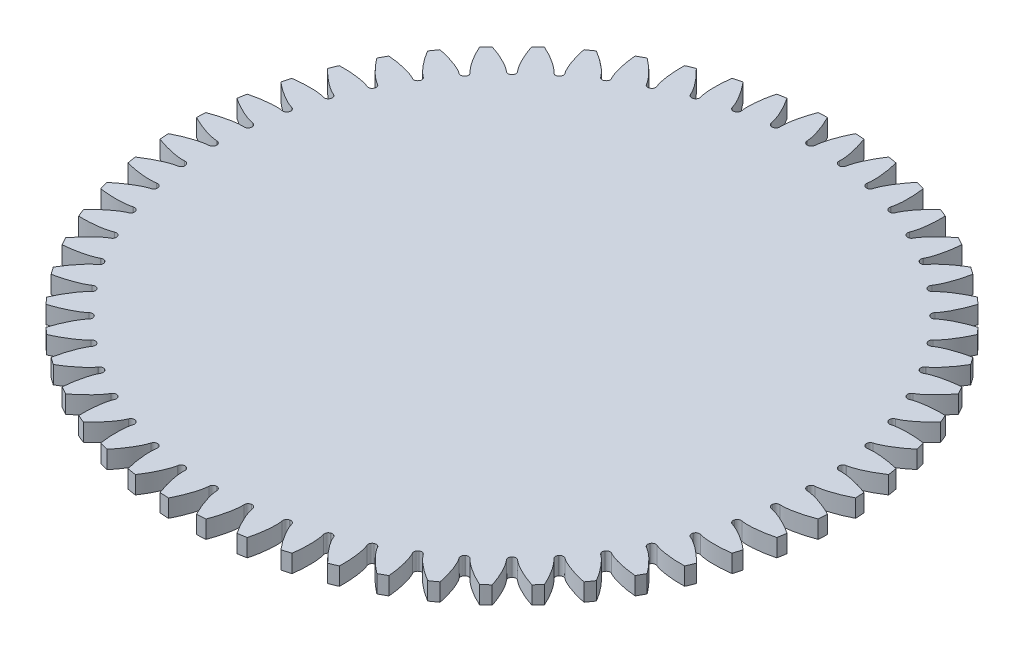
SolidWorks part; units mm, degrees
ref_plane "Front Plane" through (0, 0, 0) normal (0, 0, 1) x (1, 0, 0)
ref_plane "Top Plane" through (0, 0, 0) normal (0, 1, 0) x (1, 0, 0)
ref_plane "Right Plane" through (0, 0, 0) normal (1, 0, 0) x (0, 0, -1)
sketch "Sketch1" plane through (0, 0, 0) normal (0, 1, 0) x (1, 0, 0)
  circle A0 centre (0, 0) radius 118.3821
  dimension "D1" = 236.7643
extrude "Boss-Extrude1" add sketch "Sketch1" along normal blind 6.35
sketch "Sketch2" plane through (0, 6.35, 0) normal (0, 1, 0) x (1, 0, 0)
  line L0 (107.3976, 1.4119) -> (106.0132, 1.3937)
  line L1 (107.3976, -1.4119) -> (106.0132, -1.3937)
  line L2 (0, 0) -> (107.3976, 1.4119) construction
  line L3 (0, 0) -> (107.3976, -1.4119) construction
  arc A0 (118.2747, -5.0436) -> (118.2747, 5.0436) centre (0, 0) ccw
  circle A1 centre (0, 0) radius 114.3 construction
  circle A2 centre (0, 0) radius 107.4069 construction
  circle A3 centre (0, 0) radius 106.0223 construction
  arc A4 (106.0132, -1.3937) -> (106.0132, 1.3937) centre (0, 0) ccw
  spline S0 degree 4 poles (107.3976, 1.4119) (107.4146, 1.4123) (107.4625, 1.4139) (107.5528, 1.419) (107.7003, 1.4302) (107.8881, 1.4488) (108.1307, 1.4777) (108.4164, 1.5181) (108.7303, 1.5692) (109.0716, 1.6318) (109.4119, 1.7007) (109.7512, 1.7752) (110.089, 1.8548) (110.498, 1.9576) (110.9882, 2.0895) (111.5606, 2.2564) (112.2092, 2.4609) (112.8695, 2.6853) (113.5186, 2.9195) (114.1737, 3.1713) (114.8071, 3.4258) (115.4642, 3.7058) (116.0703, 3.9723) (116.7485, 4.2882) (117.2956, 4.5482) (118.0161, 4.9097) (118.4413, 5.1287) (118.9386, 5.3914) (119.1593, 5.5115) (119.2952, 5.5854) knots 0 0 0 0 0 0.005377 0.015084 0.028532 0.04661 0.064855 0.092111 0.119476 0.146842 0.174209 0.201575 0.228941 0.256307 0.307035 0.361767 0.4165 0.471232 0.525964 0.580697 0.635429 0.690161 0.744894 0.799626 0.854358 0.909091 0.954545 1 1 1 1 1 construction
  spline S1 degree 4 poles (107.3976, 1.4119) (107.4146, 1.4123) (107.4625, 1.4139) (107.5528, 1.419) (107.7003, 1.4302) (107.8881, 1.4488) (108.1307, 1.4777) (108.4164, 1.5181) (108.7303, 1.5692) (109.0716, 1.6318) (109.4119, 1.7007) (109.7512, 1.7752) (110.089, 1.8548) (110.498, 1.9576) (110.9882, 2.0895) (111.5606, 2.2564) (112.2092, 2.4609) (112.8695, 2.6853) (113.5186, 2.9195) (114.1737, 3.1713) (114.8071, 3.4258) (115.4642, 3.7058) (116.0703, 3.9723) (116.7485, 4.2882) (117.2956, 4.5482) (117.8599, 4.8313) (118.1344, 4.9712) (118.2747, 5.0436) knots 0 0 0 0 0 0.005377 0.015084 0.028532 0.04661 0.064855 0.092111 0.119476 0.146842 0.174209 0.201575 0.228941 0.256307 0.307035 0.361767 0.4165 0.471232 0.525964 0.580697 0.635429 0.690161 0.744894 0.799626 0.854358 0.909091 0.909091 0.909091 0.909091 0.909091
  spline S2 degree 4 poles (107.3976, -1.4119) (107.4146, -1.4123) (107.4625, -1.4139) (107.5528, -1.419) (107.7003, -1.4302) (107.8881, -1.4488) (108.1307, -1.4777) (108.4164, -1.5181) (108.7303, -1.5692) (109.0716, -1.6318) (109.4119, -1.7007) (109.7512, -1.7752) (110.089, -1.8548) (110.498, -1.9576) (110.9882, -2.0895) (111.5606, -2.2564) (112.2092, -2.4609) (112.8695, -2.6853) (113.5186, -2.9195) (114.1737, -3.1713) (114.8071, -3.4258) (115.4642, -3.7058) (116.0703, -3.9723) (116.7485, -4.2882) (117.2956, -4.5482) (118.0161, -4.9097) (118.4413, -5.1287) (118.9386, -5.3914) (119.1593, -5.5115) (119.2952, -5.5854) knots 0 0 0 0 0 0.005377 0.015084 0.028532 0.04661 0.064855 0.092111 0.119476 0.146842 0.174209 0.201575 0.228941 0.256307 0.307035 0.361767 0.4165 0.471232 0.525964 0.580697 0.635429 0.690161 0.744894 0.799626 0.854358 0.909091 0.954545 1 1 1 1 1 construction
  spline S3 degree 4 poles (107.3976, -1.4119) (107.4146, -1.4123) (107.4625, -1.4139) (107.5528, -1.419) (107.7003, -1.4302) (107.8881, -1.4488) (108.1307, -1.4777) (108.4164, -1.5181) (108.7303, -1.5692) (109.0716, -1.6318) (109.4119, -1.7007) (109.7512, -1.7752) (110.089, -1.8548) (110.498, -1.9576) (110.9882, -2.0895) (111.5606, -2.2564) (112.2092, -2.4609) (112.8695, -2.6853) (113.5186, -2.9195) (114.1737, -3.1713) (114.8071, -3.4258) (115.4642, -3.7058) (116.0703, -3.9723) (116.7485, -4.2882) (117.2956, -4.5482) (117.8599, -4.8313) (118.1344, -4.9712) (118.2747, -5.0436) knots 0 0 0 0 0 0.005377 0.015084 0.028532 0.04661 0.064855 0.092111 0.119476 0.146842 0.174209 0.201575 0.228941 0.256307 0.307035 0.361767 0.4165 0.471232 0.525964 0.580697 0.635429 0.690161 0.744894 0.799626 0.854358 0.909091 0.909091 0.909091 0.909091 0.909091
  dimension "D2" = 228.6
  dimension "D3" = 214.8137
  dimension "D4" = 212.0446
extrude "Cut-Extrude1" cut sketch "Sketch2" against normal up to next (6.35 mm away)
fillet "Fillet1" radius 1.3696 2 edges at (106.0132, 3.175, 1.3937) (106.0132, 3.175, -1.3937)
ref_axis "Axis1" through (0, 6.35, 0) along (0, -1, 0)
pattern_circular "CirPattern2" count 56 over 360 about axis through (0, 6.35, 0) along (0, -1, 0) of "Cut-Extrude1", "Fillet1"
equation "\"DiametralPitch\" = \"NumTeeth\" / 9"
equation "\"NumTeeth\" = 56"
equation "\"PressureAngle\" = 20"
equation "\"Addendum\"= 1 / \"DiametralPitch\""
equation "\"Dedendum\"= 1.25 / \"DiametralPitch\""
equation "\"WorkingDepth\"= 2 / \"DiametralPitch\""
equation "\"WholeDepth\"= 2.25 / \"DiametralPitch\""
equation "\"Clearance\"= 0.25 / \"DiametralPitch\""
equation "\"ToothThickness\"= 1.5708 / \"DiametralPitch\""
equation "\"CircularPitch\"= pi / \"DiametralPitch\""
equation "\"PitchCircle\"= \"NumTeeth\" / \"DiametralPitch\""
equation "\"OutsideDiameter\"= ( \"NumTeeth\" + 2 ) / \"DiametralPitch\""
equation "\"Fillet\"= \"Clearance\" * cos ( \"PressureAngle\" ) * tan ( ( 90 + \"PressureAngle\" ) / 2 )"
equation "\"AddendumCircle\"= \"PitchCircle\" + ( 2 * \"Addendum\" )"
equation "\"DedendumCircle\" = \"PitchCircle\" - ( 2 * \"Dedendum\" ) - .25"
equation "\"BaseCircle\"= \"PitchCircle\" * cos ( \"PressureAngle\" )"
equation "\"PitchAngle\"= 360deg / \"NumTeeth\""
equation "\"Alpha\"= sqr ( \"PitchCircle\" ^ 2 - \"BaseCircle\" ^ 2 ) / \"BaseCircle\" * 180 / PI - \"PressureAngle\""
equation "\"Beta\"= ( \"PitchAngle\" / 4 - \"Alpha\" )"
equation "\"Phi\"= sqr ( ( \"AddendumCircle\" / 2 ) ^ 2 - ( \"BaseCircle\" / 2 ) ^ 2 ) / ( \"BaseCircle\" / 2 )"
equation "\"D1@Sketch1\"=\"OutsideDiameter\""
equation "\"D2@Sketch2\"=\"PitchCircle\""
equation "\"D3@Sketch2\"=\"BaseCircle\""
equation "\"D4@Sketch2\"=\"DedendumCircle\""
equation "\"D1@Fillet1\"=\"Fillet\""
equation "\"D1@CirPattern2\"=\"NumTeeth\""
